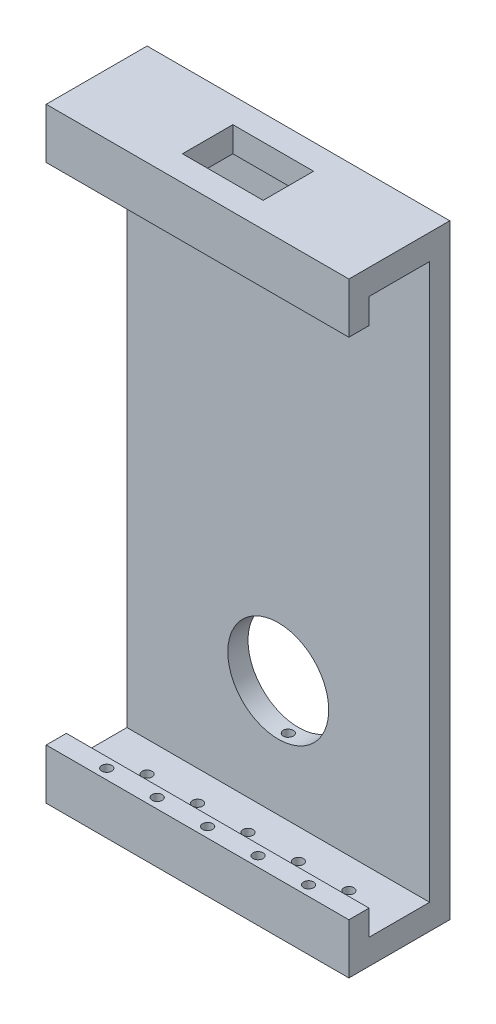
SolidWorks part; units mm, degrees
ref_plane "Plan de face" through (0, 0, 0) normal (0, 0, 1) x (1, 0, 0)
ref_plane "Plan de dessus" through (0, 0, 0) normal (0, 1, 0) x (1, 0, 0)
ref_plane "Plan de droite" through (0, 0, 0) normal (1, 0, 0) x (0, 0, -1)
sketch "Esquisse1" plane through (0, 0, 0) normal (0, 0, 1) x (1, 0, 0)
  line L1 (8.4633, 120) -> (68.4633, 120)
  line L2 (8.4633, 120) -> (8.4633, 0)
  line L3 (8.4633, 0) -> (68.4633, 0)
  line L4 (68.4633, 120) -> (68.4633, 0)
  dimension "D1" = 120
  dimension "D2" = 60
extrude "Boss.-Extru.1" add sketch "Esquisse1" along normal blind 20
sketch "Esquisse2" plane through (68.4633, 0, 0) normal (1, 0, 0) x (0, 0, -1)
  line L0 (-20, 110) -> (-16, 110)
  line L1 (-20, 0) -> (-20, 120) construction
  line L2 (-16, 110) -> (-16, 115)
  line L3 (-16, 115) -> (-4, 115)
  line L4 (-4, 115) -> (-4, 5)
  line L5 (-4, 5) -> (-16, 5)
  line L6 (-16, 5) -> (-16, 10)
  line L7 (-16, 10) -> (-20, 10)
  line L8 (-20, 10) -> (-20, 110)
  line L9 (-20, 120) -> (0, 120) construction
  line L10 (0, 0) -> (0, 120) construction
  line L11 (-20, 0) -> (0, 0) construction
  dimension "D1" = 5
  dimension "D2" = 4
  dimension "D3" = 5
  dimension "D4" = 4
  dimension "D5" = 5
extrude "Enlèv. mat.-Extru.1" cut sketch "Esquisse2" against normal through all
sketch "Esquisse3" plane through (0, 120, 0) normal (0, 1, 0) x (1, 0, 0)
  line L0 (68.4633, 0) -> (8.4633, 0) construction
  line L1 (30.4633, -5) -> (46.4633, -5)
  line L2 (30.4633, -5) -> (30.4633, -15)
  line L3 (30.4633, -15) -> (46.4633, -15)
  line L4 (46.4633, -5) -> (46.4633, -15)
  point P6 (38.4633, 0)
  point P7 (38.4633, -5)
  point P8 (0, 0)
  dimension "D1" = 5
  dimension "D2" = 10
  dimension "D3" = 16
extrude "Enlèv. mat.-Extru.3" cut sketch "Esquisse3" against normal up to surface (5 mm away) up to face at (38.4633, 115, 10)
sketch "Esquisse4" plane through (0, 0, 0) normal (0, 0, -1) x (-1, 0, 0)
  line L0 (-8.4633, 0) -> (-68.4633, 0) construction
  circle A0 centre (-38.4633, 28) radius 10
  point P2 (-38.4633, 0)
  point P3 (0, 0)
  dimension "D1" = 20
  dimension "D2" = 28
extrude "Enlèv. mat.-Extru.4" cut sketch "Esquisse4" against normal through all
sketch "Esquisse5" plane through (0, 0, 0) normal (0, -1, 0) x (1, 0, 0)
  line L0 (8.4633, 20) -> (68.4633, 20) construction
  line L1 (8.4633, 0) -> (68.4633, 0) construction
  line L2 (68.4633, 20) -> (68.4633, 0) construction
  circle A0 centre (38.4633, 18) radius 1
  circle A1 centre (38.4633, 2) radius 1
  circle A2 centre (38.4633, 10) radius 1
  point P2 (38.4633, 20)
  point P7 (0, 0)
  point P12 (0, 0)
  point P15 (68.4633, 10)
  dimension "D1" = 2
  dimension "D2" = 2
  dimension "D3" = 2
extrude "Enlèv. mat.-Extru.5" cut sketch "Esquisse5" against normal blind 20
pattern_linear "Répétition linéaire1" count 3 spacing 10 along (1, 0, 0) of "Enlèv. mat.-Extru.5"
pattern_linear "Répétition linéaire2" count 3 spacing 10 along (-1, 0, 0) of "Enlèv. mat.-Extru.5"
